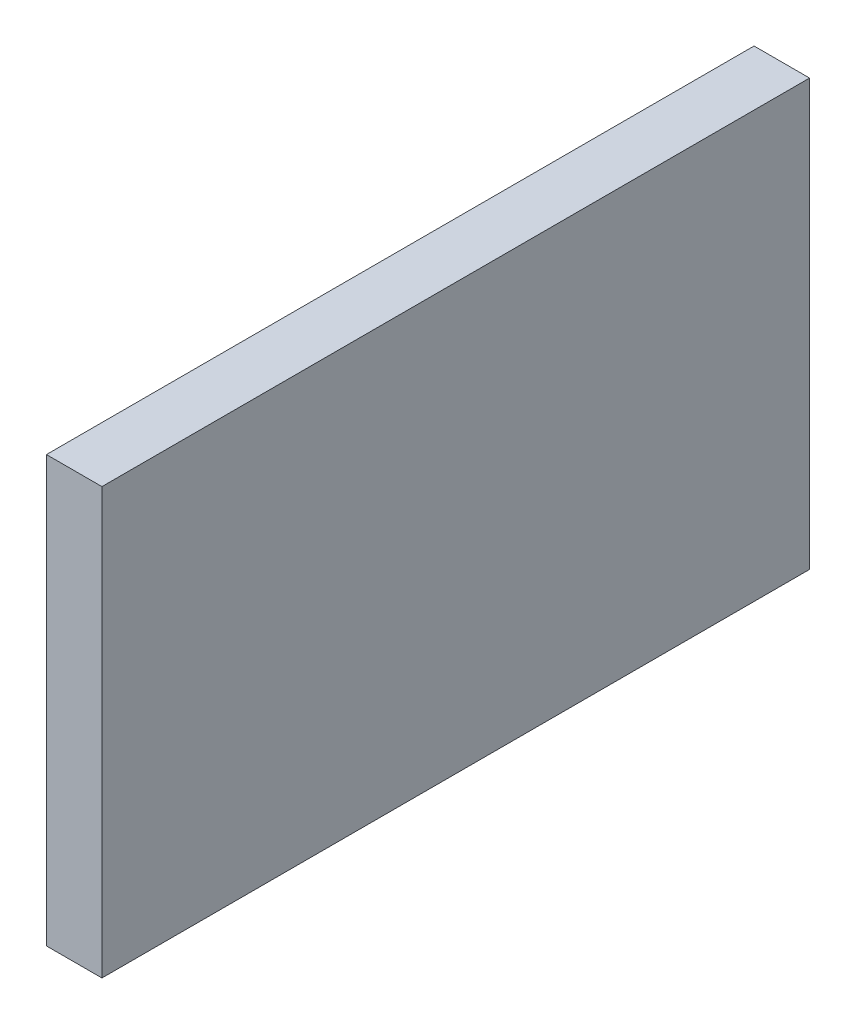
SolidWorks part; units mm, degrees
material "Acrylic (Medium-high impact)"
ref_plane "Front Plane" through (0, 0, 0) normal (0, 0, 1) x (1, 0, 0)
ref_plane "Top Plane" through (0, 0, 0) normal (0, 1, 0) x (1, 0, 0)
ref_plane "Right Plane" through (0, 0, 0) normal (1, 0, 0) x (0, 0, -1)
sketch "Sketch1" plane through (0, 0, 76.0305) normal (0, 0, -1) x (-1, 0, 0)
  line L0 (-51.9215, 21.8233) -> (-56.9215, 21.8233) construction
  line L1 (-56.3577, 44.8268) -> (-53.3577, 44.8268)
  line L2 (-56.3577, 44.8268) -> (-56.3577, 21.8233)
  line L3 (-56.3577, 21.8233) -> (-53.3577, 21.8233)
  line L4 (-53.3577, 44.8268) -> (-53.3577, 21.8233)
  dimension "D1" = 3
extrude "Boss-Extrude1" add sketch "Sketch1" along normal up to surface (38.25 mm away)
